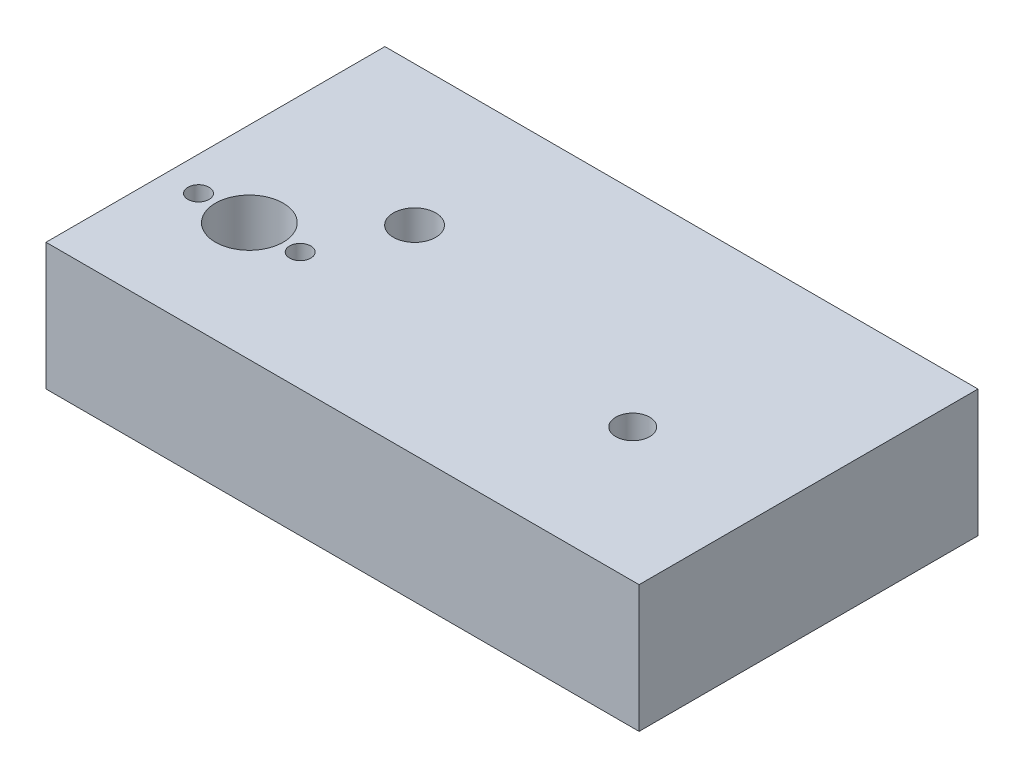
SolidWorks part; units mm, degrees
ref_plane "Front Plane" through (0, 0, 0) normal (0, 0, 1) x (1, 0, 0)
ref_plane "Top Plane" through (0, 0, 0) normal (0, 1, 0) x (1, 0, 0)
ref_plane "Right Plane" through (0, 0, 0) normal (1, 0, 0) x (0, 0, -1)
sketch "Sketch1" plane through (0, 0, 0) normal (0, 0, 1) x (1, 0, 0)
  line L1 (-45.1303, 23.1413) -> (94.8697, 23.1413)
  line L2 (-45.1303, 23.1413) -> (-45.1303, -6.8587)
  line L3 (-45.1303, -6.8587) -> (94.8697, -6.8587)
  line L4 (94.8697, 23.1413) -> (94.8697, -6.8587)
  dimension "D1" = 140
  dimension "D2" = 30
extrude "Boss-Extrude1" add sketch "Sketch1" along normal blind 80
sketch "Sketch2" plane through (0, 0, 0) normal (0, 0, -1) x (-1, 0, 0)
  line L0 (45.1303, -6.8587) -> (-94.8697, -6.8587) construction
  line L1 (45.1303, 23.1413) -> (45.1303, -6.8587) construction
  circle A0 centre (30.1303, 7.8145) radius 4.1759
  dimension "D1" = 14.6732
  dimension "D2" = 15
extrude "Cut-Extrude1" cut sketch "Sketch2" against normal blind 15
pattern_linear "LPattern1" count 4 spacing 110 along (1, 0, 0) of "Cut-Extrude1"
sketch "Эскиз1" plane through (0, -6.8587, 0) normal (0, -1, 0) x (1, 0, 0)
  line L0 (-45.1303, 80) -> (-45.1303, 0) construction
  line L1 (-45.1303, 0) -> (94.8697, 0) construction
  circle A0 centre (-5.1303, 33) radius 25
  dimension "D3" = 50
  dimension "D1" = 40
  dimension "D2" = 33
extrude "Вырез-Вытянуть1" cut sketch "Эскиз1" against normal blind 10.5
sketch "Эскиз2" plane through (0, 3.6413, 0) normal (0, -1, 0) x (1, 0, 0)
  circle A0 centre (-5.1303, 33) radius 5
  circle A1 centre (-5.1303, 33) radius 25 construction
  dimension "D1" = 10
extrude "Вырез-Вытянуть2" cut sketch "Эскиз2" against normal blind 100 and the other way blind 10
sketch "Эскиз3" plane through (0, -6.8587, 0) normal (0, -1, 0) x (1, 0, 0)
  line L0 (-45.1303, 80) -> (-45.1303, 0) construction
  line L1 (-45.1303, 80) -> (94.8697, 80) construction
  circle A0 centre (-25.1303, 52) radius 8
  dimension "D3" = 16
  dimension "D1" = 20
  dimension "D2" = 28
extrude "Вырез-Вытянуть3" cut sketch "Эскиз3" against normal blind 100
sketch "Эскиз4" plane through (0, -6.8587, 0) normal (0, -1, 0) x (1, 0, 0)
  circle A0 centre (-25.1303, 52) radius 10
extrude "Вырез-Вытянуть4" cut sketch "Эскиз4" against normal blind 10.5
sketch "Эскиз5" plane through (0, 23.1413, 0) normal (0, 1, 0) x (1, 0, 0)
  line L1 (94.8697, -80) -> (-45.1303, -80) construction
  circle A0 centre (-37.1303, -52) radius 2.5
  circle A1 centre (-25.1303, -52) radius 8 construction
  dimension "D1" = 12
  dimension "D2" = 28
  dimension "D3" = 5
extrude "Вырез-Вытянуть5" cut sketch "Эскиз5" against normal blind 100
pattern_linear "Линейный массив1" count 2 spacing 24 along (1, 0, 0) of "Вырез-Вытянуть5"
sketch "Эскиз6" plane through (0, 23.1413, 0) normal (0, 1, 0) x (1, 0, 0)
  line L0 (94.8697, -80) -> (-45.1303, -80) construction
  line L1 (94.8697, -80) -> (94.8697, 0) construction
  circle A0 centre (61.8697, -48.5) radius 4
  dimension "D1" = 8
  dimension "D2" = 31.5
  dimension "D3" = 33
extrude "Вырез-Вытянуть6" cut sketch "Эскиз6" against normal blind 100
